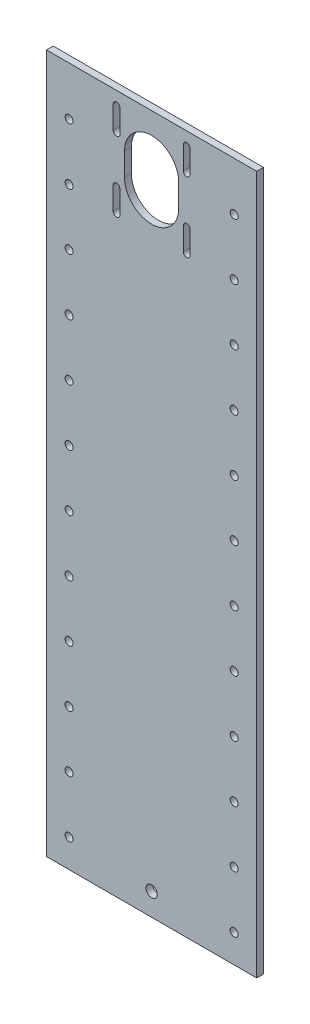
SolidWorks part; units mm, degrees
ref_plane "Plan de face" through (0, 0, 0) normal (0, 0, 1) x (1, 0, 0)
ref_plane "Plan de dessus" through (0, 0, 0) normal (0, 1, 0) x (1, 0, 0)
ref_plane "Plan de droite" through (0, 0, 0) normal (1, 0, 0) x (0, 0, -1)
sketch "Esquisse1" plane through (0, 0, 0) normal (0, 0, 1) x (1, 0, 0)
  line L1 (0, 0) -> (93, 0)
  line L2 (0, 0) -> (0, 309)
  line L3 (0, 309) -> (93, 309)
  line L4 (93, 0) -> (93, 309)
  dimension "D1" = 309
  dimension "D2" = 93
extrude "Boss.-Extru.1" add sketch "Esquisse1" along normal blind 3
sketch "Esquisse2" plane through (0, 0, 3) normal (0, 0, 1) x (1, 0, 0)
  line L0 (31, 293) -> (62, 262) construction
  line L1 (31, 293) -> (62, 293) construction
  line L2 (31, 293) -> (31, 262) construction
  line L3 (31, 262) -> (62, 262) construction
  line L4 (62, 293) -> (62, 262) construction
  line L5 (62, 293) -> (31, 262) construction
  line L6 (46.5, 277.5) -> (46.5, 287.5) construction
  line L7 (34.5, 277.5) -> (34.5, 287.5)
  line L8 (58.5, 277.5) -> (58.5, 287.5)
  line L9 (31, 293) -> (31, 303) construction
  line L10 (29.5, 293) -> (29.5, 303)
  line L11 (32.5, 293) -> (32.5, 303)
  line L12 (62, 293) -> (62, 303) construction
  line L13 (60.5, 293) -> (60.5, 303)
  line L14 (63.5, 293) -> (63.5, 303)
  line L15 (62, 262) -> (62, 272) construction
  line L16 (60.5, 262) -> (60.5, 272)
  line L17 (63.5, 262) -> (63.5, 272)
  line L18 (31, 262) -> (31, 272) construction
  line L19 (29.5, 262) -> (29.5, 272)
  line L20 (32.5, 262) -> (32.5, 272)
  line L21 (46.5, 293) -> (46.5, 309) construction
  line L22 (93, 309) -> (0, 309) construction
  line L23 (31, 303) -> (62, 303) construction
  arc A0 (34.5, 277.5) -> (58.5, 277.5) centre (46.5, 277.5) ccw
  arc A1 (58.5, 287.5) -> (34.5, 287.5) centre (46.5, 287.5) ccw
  arc A2 (29.5, 293) -> (32.5, 293) centre (31, 293) ccw
  arc A3 (32.5, 303) -> (29.5, 303) centre (31, 303) ccw
  arc A4 (60.5, 293) -> (63.5, 293) centre (62, 293) ccw
  arc A5 (63.5, 303) -> (60.5, 303) centre (62, 303) ccw
  arc A6 (60.5, 262) -> (63.5, 262) centre (62, 262) ccw
  arc A7 (63.5, 272) -> (60.5, 272) centre (62, 272) ccw
  arc A8 (29.5, 262) -> (32.5, 262) centre (31, 262) ccw
  arc A9 (32.5, 272) -> (29.5, 272) centre (31, 272) ccw
  point P4 (46.5, 282.5)
  point P11 (31, 298)
  point P17 (62, 298)
  point P23 (62, 267)
  point P29 (31, 267)
  dimension "D1" = 24
  dimension "D2" = 31
  dimension "D3" = 3
  dimension "D4" = 10
  dimension "D5" = 6
extrude "Persage Stepper" cut sketch "Esquisse2" against normal through all
sketch "Esquisse3" plane through (0, 0, 3) normal (0, 0, 1) x (1, 0, 0)
  line L0 (46.5, 10) -> (46.5, 0) construction
  line L1 (0, 0) -> (93, 0) construction
  circle A0 centre (46.5, 10) radius 2.5
  dimension "D1" = 5
  dimension "D2" = 10
extrude "Enlèv. mat.-Extru.1" cut sketch "Esquisse3" against normal up to surface (3 mm away) up to face at (31, 267, 0)
sketch "Esquisse4" plane through (0, 0, 3) normal (0, 0, 1) x (1, 0, 0)
  line L0 (46.5, 0) -> (46.5, 12.5) construction
  line L1 (0, 0) -> (93, 0) construction
  line L2 (10, 12.5) -> (83, 12.5) construction
  circle A0 centre (10, 12.5) radius 1.75
  circle A1 centre (83, 12.5) radius 1.75
  circle A2 centre (10, 37.5) radius 1.75
  circle A3 centre (83, 37.5) radius 1.75
  circle A4 centre (10, 62.5) radius 1.75
  circle A5 centre (83, 62.5) radius 1.75
  circle A6 centre (10, 87.5) radius 1.75
  circle A7 centre (83, 87.5) radius 1.75
  circle A8 centre (10, 112.5) radius 1.75
  circle A9 centre (83, 112.5) radius 1.75
  circle A10 centre (10, 137.5) radius 1.75
  circle A11 centre (83, 137.5) radius 1.75
  circle A12 centre (10, 162.5) radius 1.75
  circle A13 centre (83, 162.5) radius 1.75
  circle A14 centre (10, 187.5) radius 1.75
  circle A15 centre (83, 187.5) radius 1.75
  circle A16 centre (10, 212.5) radius 1.75
  circle A17 centre (83, 212.5) radius 1.75
  circle A18 centre (10, 237.5) radius 1.75
  circle A19 centre (83, 237.5) radius 1.75
  circle A20 centre (10, 262.5) radius 1.75
  circle A21 centre (83, 262.5) radius 1.75
  circle A22 centre (10, 287.5) radius 1.75
  circle A23 centre (83, 287.5) radius 1.75
  point P7 (46.5, 12.5)
  dimension "D2" = 3.5
  dimension "D3" = 3.5
  dimension "D1" = 73
  dimension "D4" = 12.5
  dimension "D5" = 12
extrude "Enlèv. mat.-Extru.2" cut sketch "Esquisse4" against normal up to surface (3 mm away) up to face at (44, 10, 0)
